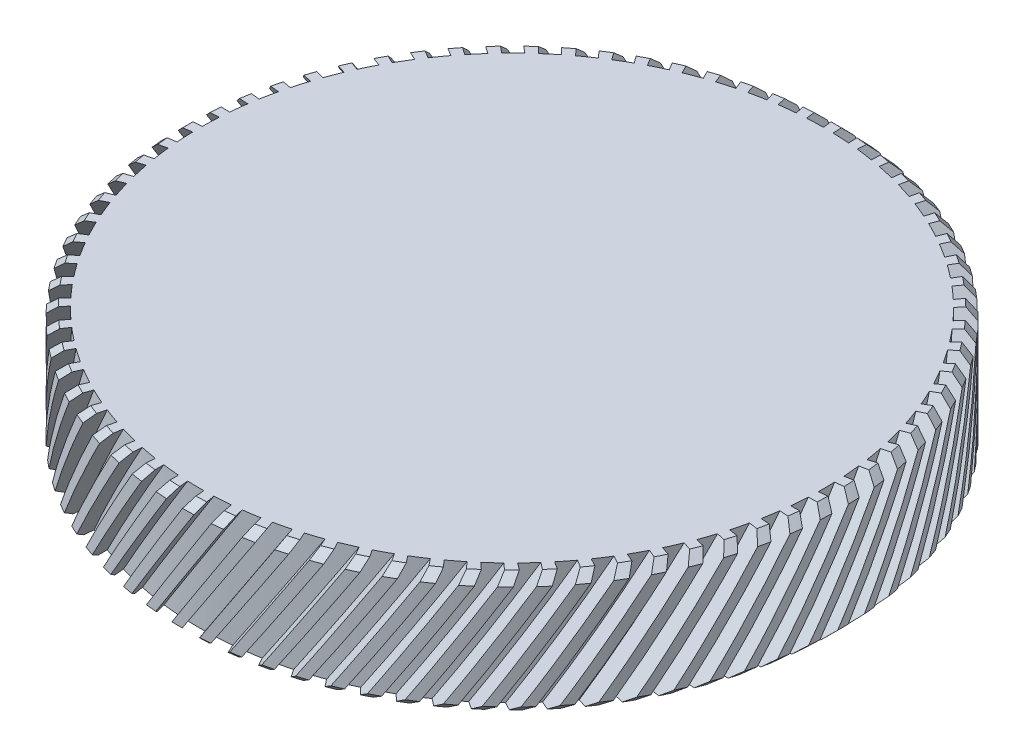
SolidWorks part; units mm, degrees
ref_plane "前视基准面" through (0, 0, 0) normal (0, 0, 1) x (1, 0, 0)
ref_plane "上视基准面" through (0, 0, 0) normal (0, 1, 0) x (1, 0, 0)
ref_plane "右视基准面" through (0, 0, 0) normal (1, 0, 0) x (0, 0, -1)
sketch "草图1" plane through (0, 0, 0) normal (0, 0, 1) x (1, 0, 0)
  line L0 (0, 46.0207) -> (0, -69.6142) construction
  line L1 (17, -8.8309) -> (17.6, -8.8309)
  line L2 (19.05, -6.3309) -> (0, -6.3309)
  line L3 (17, -13.3309) -> (19.05, -13.3309)
  line L4 (17, -13.3309) -> (17, -8.8309)
  line L5 (17.6, -8.8309) -> (17.6, -7.8309)
  line L6 (19.05, -13.3309) -> (19.05, -6.3309)
  line L7 (17.6, -7.8309) -> (0, -7.8309)
  line L8 (0, -7.8309) -> (0, -6.3309)
  dimension "D1" = 17.6
  dimension "D2" = 7
  dimension "D3" = 19.05
  dimension "D4" = 17
  dimension "D5" = 4.5
  dimension "D6" = 5.5
revolve "旋转1" add sketch "草图1" angle 360 about L0
cosmetic thread "装饰螺纹线1" parameters "D2"=35
chamfer "倒角1" distance 0.5 angle 45 2 edges at (0, -6.3309, 19.05) (0, -13.3309, 19.05)
surface "曲面-等距1" parameters "D1"=1
sketch "草图2" plane through (0, 0, 0) normal (0, 0, 1) x (1, 0, 0)
  line L0 (0, -2.7759) -> (-6.5923, -13.3309)
  line L1 (0, -2.7759) -> (0.6785, -3.1997)
  line L2 (-6.5923, -13.3309) -> (-5.9138, -13.7547)
  line L3 (0.6785, -3.1997) -> (-5.9138, -13.7547)
  line L4 (-18.55, -13.3309) -> (18.55, -13.3309) construction
extrude "切除-拉伸1" cut sketch "草图2" against normal up to surface (11.95 mm away) from offset 30
pattern_circular "阵列(圆周)1" count 75 over 360 about axis through (0, 0, 0) along (0, 1, 0) of "切除-拉伸1"
delete or keep bodies "实体-删除/保留 1" type delete bodies bodies 107
